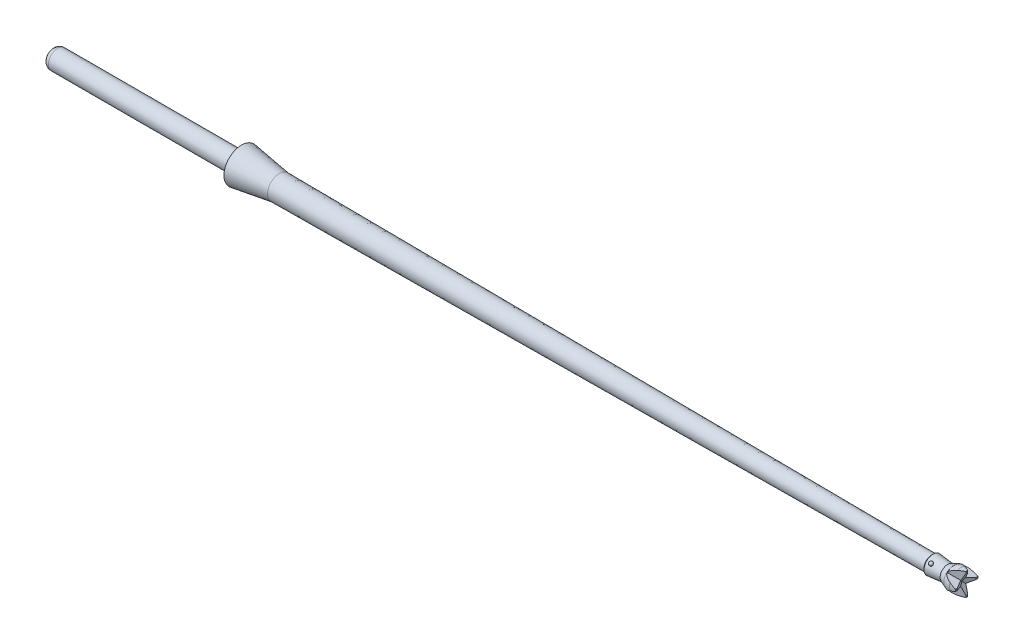
SolidWorks part; units mm, degrees
ref_plane "Front Plane" through (0, 0, 0) normal (0, 0, 1) x (1, 0, 0)
ref_plane "Top Plane" through (0, 0, 0) normal (0, 1, 0) x (1, 0, 0)
ref_plane "Right Plane" through (0, 0, 0) normal (1, 0, 0) x (0, 0, -1)
sketch "Sketch1" plane through (0, 0, 0) normal (0, 0, 1) x (1, 0, 0)
  line L0 (0, 1) -> (0, 1.85)
  line L1 (0, 0) -> (-20, 0)
  line L2 (0, 0) -> (0, 1) construction
  line L3 (0, 1) -> (-20, 1)
  line L4 (-20, 0) -> (-20, 1)
  line L5 (0, 1.85) -> (4, 1.25)
  line L6 (4, 1.25) -> (72.9, 0.8)
  line L7 (72.9, 0.8) -> (73.05, 0.95)
  line L8 (73.05, 0.95) -> (74.6, 0.8)
  line L9 (74.6, 0.8) -> (75.6, 1.2)
  line L10 (75.6, 1.2) -> (76.6, 1.2)
  line L11 (76.6, 1.2) -> (76.6, 0)
  line L12 (76.6, 0) -> (0, 0)
  dimension "D1" = 20
  dimension "D2" = 1
  dimension "D3" = 1.85
  dimension "D4" = 4
  dimension "D5" = 1.25
  dimension "D6" = 72.9
  dimension "D7" = 0.8
  dimension "D8" = 0.95
  dimension "D9" = 1.7
  dimension "D10" = 45
  dimension "D11" = 0.8
  dimension "D12" = 1.2
  dimension "D13" = 2
  dimension "D14" = 1
  dimension "D15" = 76.6
revolve "Revolve1" add sketch "Sketch1" angle 360 about L12
fillet "Fillet1" radius 2 1 edges at (75.6, 0, -1.2)
sketch "Sketch2" plane through (0, 0, 0) normal (0, 0, 1) x (1, 0, 0)
  line L0 (0, 0) -> (76.6, 0) construction
  line L1 (76.6, -1.2) -> (76.6, 1.2) construction
  line L2 (76.6, 0.1) -> (75.3, 0.697)
  line L3 (75.3, 0.697) -> (75.3, 1.3)
  line L4 (75.3, 1.3) -> (76.6, 1.3)
  line L5 (76.6, 1.3) -> (76.6, 0.1)
  dimension "D1" = 0.1
  dimension "D2" = 0.697
  dimension "D3" = 1.3
  dimension "D4" = 1.3
extrude "Cut-Extrude1" cut sketch "Sketch2" against normal through all both and the other way through all
mirror "Mirror1" about plane through (0, 0, 0) normal (0, 1, 0) of "Cut-Extrude1"
sketch "Sketch3" plane through (0, 0, 0) normal (0, 1, 0) x (1, 0, 0)
  line L0 (0, 0) -> (76.6, 0) construction
  line L1 (76.6, 1.1958) -> (76.6, -1.1958) construction
  line L2 (76.6, 1) -> (76.6, -1)
  line L3 (76.6, 1) -> (76.1, 0)
  line L4 (76.1, 0) -> (76.6, -1)
  dimension "D1" = 1
  dimension "D2" = 1
  dimension "D3" = 0.5
extrude "Cut-Extrude2" cut sketch "Sketch3" against normal through all both and the other way through all
ref_plane "Plane1" through (74.6, 0, 0) normal (1, 0, 0) x (0, 0, -1)
split "Split1" trim tools "Plane1" bodies to split 104 resulting bodies 105 106
move or copy body "Body-Move/Copy1" bodies to move or copy 105 copy yes number of copies 1 rotation origin (0, 0, -0.0154) rotation axis (1, 0, 0) rotation angle 90
combine bodies "Combine1" operation type add bodies to combine 106 107 105
fillet "Fillet2" radius 0.6 1 edges at (-20, 0, -1)
sketch "Sketch5" plane through (0, 0, 0) normal (0, 0, 1) x (1, 0, 0)
  line L0 (74.6, 0.8) -> (73.05, 0.95) construction
  line L1 (74.6, 0.8) -> (73.05, 0.95) construction
  line L2 (73.5, 1.1065) -> (73.5, 0.7065)
  arc A0 (73.5, 0.7065) -> (73.5, 1.1065) centre (73.5, 0.9065) ccw
  dimension "D1" = 0.4
  dimension "D2" = 73.5
revolve "Revolve2" add sketch "Sketch5" angle 360 about L2
move or copy body "Body-Move/Copy2" bodies to move or copy 109 copy no rotation origin (0, -0.0154, 0) rotation axis (1, 0, 0) rotation angle 45
move or copy body "Body-Move/Copy3" bodies to move or copy 110 copy yes number of copies 1 rotation origin (0, -0.0154, 0) rotation axis (1, 0, 0) rotation angle 180
